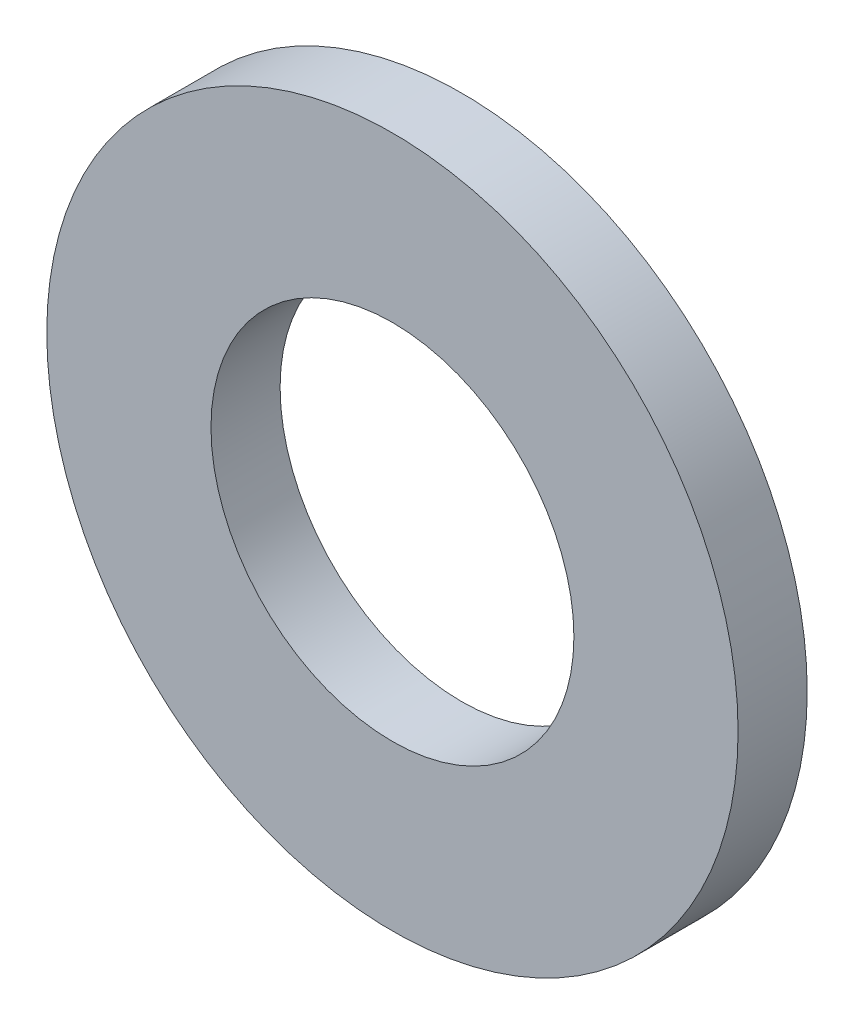
SolidWorks part; units mm, degrees
material "Сталь"
ref_plane "Спереди" through (0, 0, 0) normal (0, 0, 1) x (1, 0, 0)
ref_plane "Сверху" through (0, 0, 0) normal (0, 1, 0) x (1, 0, 0)
ref_plane "Справа" through (0, 0, 0) normal (1, 0, 0) x (0, 0, -1)
sketch "Эскиз1" plane through (0, 0, 0) normal (0, 0, 1) x (1, 0, 0)
  circle A0 centre (0, 0) radius 4.2
  circle A1 centre (0, 0) radius 8
  dimension "D1" = 8.4
  dimension "D2" = 16
extrude "Бобышка-Вытянуть1" add sketch "Эскиз1" along normal blind 1.6
